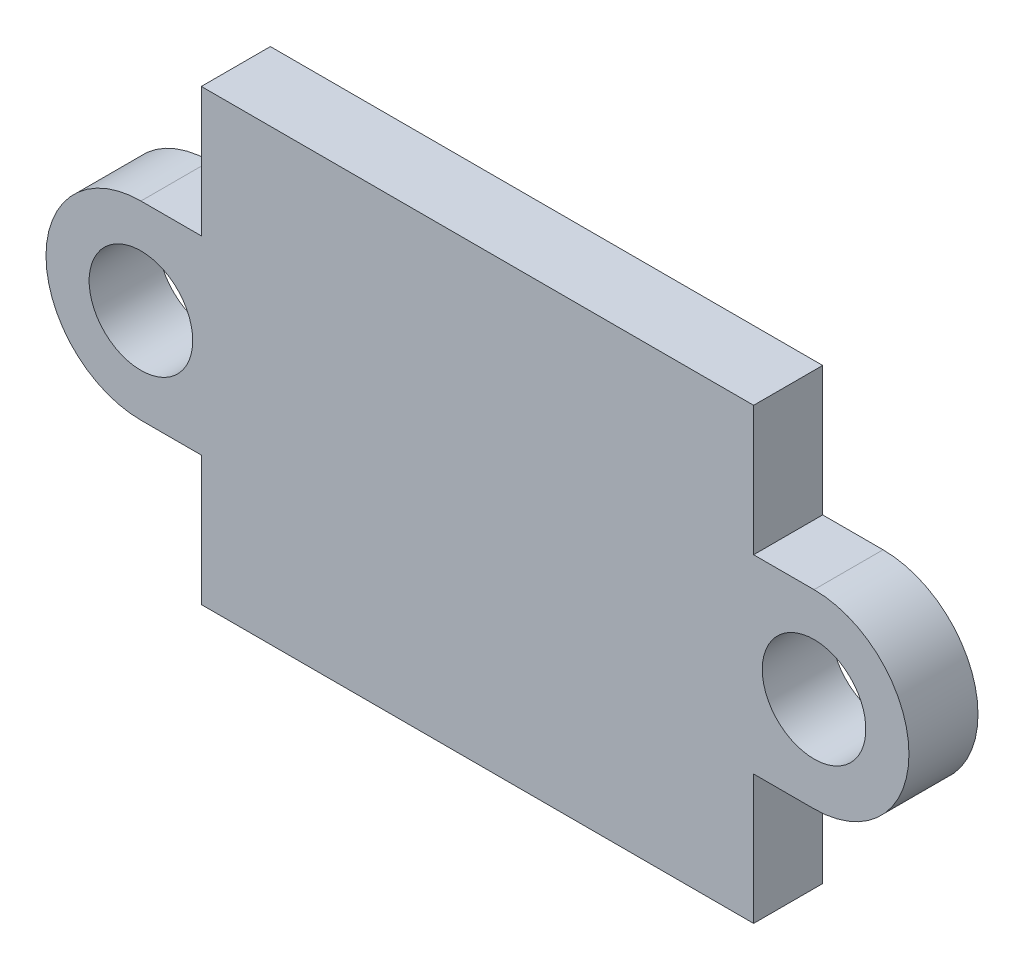
SolidWorks part; units mm, degrees
ref_plane "Plano frontal" through (0, 0, 0) normal (0, 0, 1) x (1, 0, 0)
ref_plane "Plano superior" through (0, 0, 0) normal (0, 1, 0) x (1, 0, 0)
ref_plane "Plano direito" through (0, 0, 0) normal (1, 0, 0) x (0, 0, -1)
sketch "Sketch1" plane through (0, 0, 0) normal (0, 0, 1) x (1, 0, 0)
  line L1 (8, -6.5) -> (-8, -6.5)
  line L2 (8, -6.5) -> (8, 6.5)
  line L3 (8, 6.5) -> (-8, 6.5)
  line L4 (-8, -6.5) -> (-8, 6.5)
  line L5 (8, -6.5) -> (-8, 6.5) construction
  line L6 (8, 6.5) -> (-8, -6.5) construction
  point P0 (0, 0)
  dimension "D1" = 16
  dimension "D2" = 13
extrude "Boss-Extrude1" add sketch "Sketch1" along normal mid plane 2
sketch "Sketch2" plane through (0, 0, 0) normal (0, 0, 1) x (1, 0, 0)
  line L0 (0, -1.1) -> (0, 1.1) construction
  line L1 (-9.75, 2.75) -> (-9.75, -2.75) construction
  line L2 (-9.75, 2.75) -> (-8, 2.75)
  line L3 (-8, 6.5) -> (-8, -6.5) construction
  line L4 (-9.75, -2.75) -> (-8, -2.75)
  line L5 (9.75, -2.75) -> (8, -2.75)
  line L6 (9.75, 2.75) -> (8, 2.75)
  line L7 (-8, 2.75) -> (-8, -2.75)
  line L8 (8, 2.75) -> (8, -2.75)
  circle A0 centre (-9.75, 0) radius 1.5
  circle A1 centre (9.75, 0) radius 1.5
  arc A2 (-9.75, 2.75) -> (-9.75, -2.75) centre (-9.75, 0) ccw
  arc A3 (9.75, 2.75) -> (9.75, -2.75) centre (9.75, 0) cw
  dimension "D1" = 3
  dimension "D2" = 25
  dimension "D3" = 1.25
  dimension "D4" = 19.5
extrude "Boss-Extrude2" add sketch "Sketch2" along normal mid plane 2
